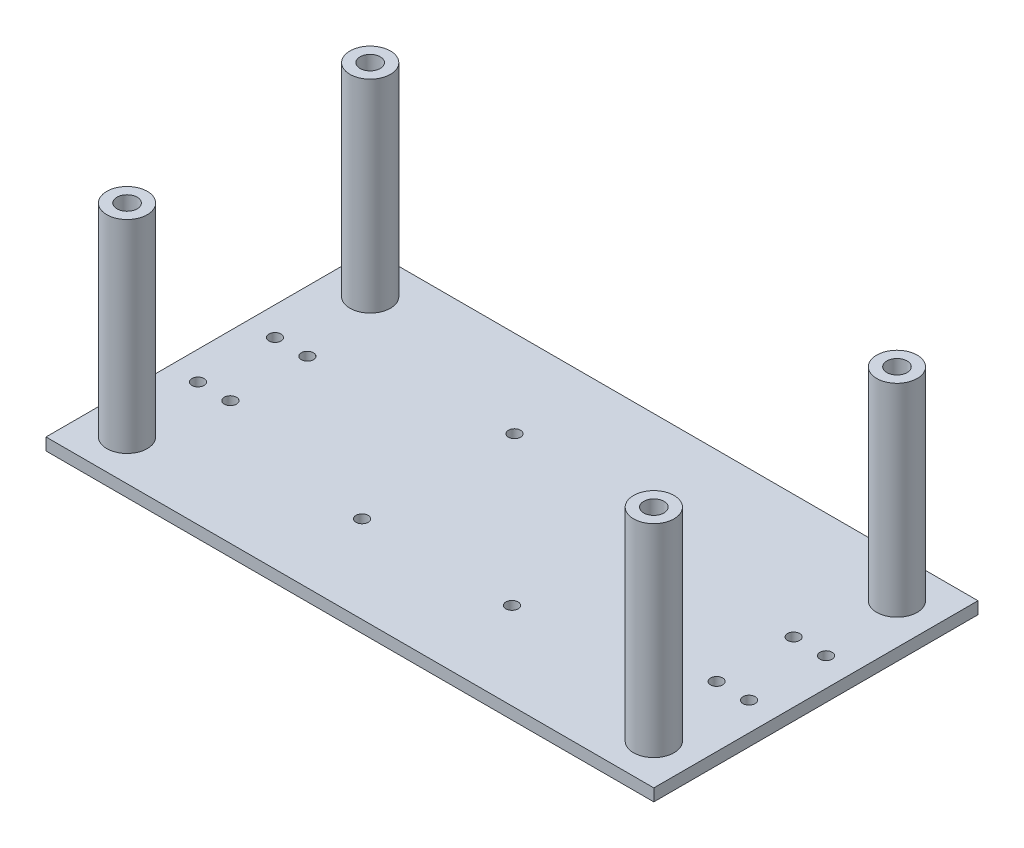
SolidWorks part; units mm, degrees
ref_plane "Front Plane" through (0, 0, 0) normal (0, 0, 1) x (1, 0, 0)
ref_plane "Top Plane" through (0, 0, 0) normal (0, 1, 0) x (1, 0, 0)
ref_plane "Right Plane" through (0, 0, 0) normal (1, 0, 0) x (0, 0, -1)
sketch "Sketch2" plane through (0, 0, 0) normal (0, 1, 0) x (1, 0, 0)
  line L0 (-83.4647, 1.8257) -> (66.5353, 1.8257)
  line L1 (-83.4647, 41.8257) -> (66.5353, 41.8257)
  line L2 (-83.4647, 41.8257) -> (-83.4647, -38.1743)
  line L3 (-83.4647, -38.1743) -> (66.5353, -38.1743)
  line L4 (66.5353, 41.8257) -> (66.5353, -38.1743)
  circle A0 centre (-68.4647, 11.3257) radius 1.5
  circle A1 centre (-68.4647, -7.6743) radius 1.5
  circle A2 centre (-76.4647, 11.3257) radius 1.5
  circle A3 centre (-76.4647, -7.6743) radius 1.5
  circle A4 centre (51.5353, -7.6743) radius 1.5
  circle A5 centre (59.5353, -7.6743) radius 1.5
  circle A6 centre (59.5353, 11.3257) radius 1.5
  circle A7 centre (51.5353, 11.3257) radius 1.5
  dimension "D3" = 3
  dimension "D7" = 3
  dimension "D1" = 80
  dimension "D2" = 150
  dimension "D4" = 19
  dimension "D5" = 15
  dimension "D6" = 9.5
  dimension "D8" = 7
  dimension "D9" = 7
  dimension "D10" = 15
extrude "Boss-Extrude1" add sketch "Sketch2" against normal blind 3 contours L4 L0 L2 L3 A3 A1 | L4 L1 L2 L0 A2 A0
sketch "Sketch3" plane through (0, 0, 0) normal (0, 1, 0) x (1, 0, 0)
  line L0 (-83.4647, 41.8257) -> (-83.4647, -38.1743) construction
  line L1 (-83.4647, 41.8257) -> (66.5353, 41.8257) construction
  line L2 (-83.4647, -38.1743) -> (66.5353, -38.1743) construction
  line L3 (66.5353, 41.8257) -> (66.5353, -38.1743) construction
  circle A0 centre (-73.4647, 31.8257) radius 5
  circle A1 centre (56.5353, 31.8257) radius 5
  circle A2 centre (56.5353, -28.1743) radius 5
  circle A3 centre (-73.4647, -28.1743) radius 5
  circle A4 centre (56.5353, 31.8257) radius 2.5
  circle A5 centre (56.5353, -28.1743) radius 2.5
  circle A6 centre (-73.4647, -28.1743) radius 2.5
  circle A7 centre (-73.4647, 31.8257) radius 2.5
  dimension "D1" = 10
  dimension "D10" = 5
  dimension "D2" = 10
  dimension "D3" = 10
  dimension "D4" = 10
  dimension "D5" = 10
  dimension "D6" = 10
  dimension "D7" = 10
  dimension "D8" = 10
  dimension "D9" = 10
extrude "Boss-Extrude2" add sketch "Sketch3" along normal blind 50
sketch "Sketch4" plane through (0, -3, 0) normal (0, -1, 0) x (1, 0, 0)
  circle A0 centre (-26.9647, 16.6743) radius 1.5
  circle A1 centre (10.0353, 16.6743) radius 1.5
  circle A2 centre (10.0353, -20.3257) radius 1.5
  circle A3 centre (-26.3532, -20.3257) radius 1.5
  dimension "D5" = 3
  dimension "D1" = 37
  dimension "D2" = 37
extrude "Cut-Extrude1" cut sketch "Sketch4" against normal blind 10
